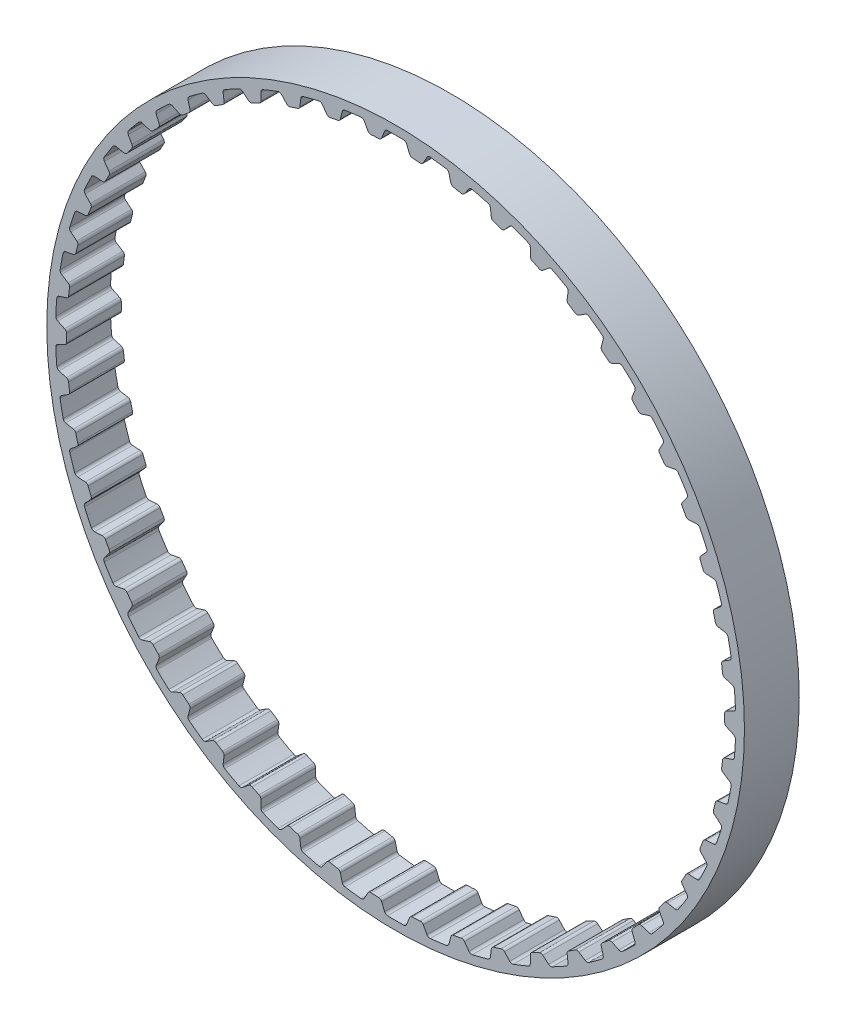
SolidWorks part; units mm, degrees
ref_plane "Front Plane" through (0, 0, 0) normal (0, 0, 1) x (1, 0, 0)
ref_plane "Top Plane" through (0, 0, 0) normal (0, 1, 0) x (1, 0, 0)
ref_plane "Right Plane" through (0, 0, 0) normal (1, 0, 0) x (0, 0, -1)
sketch "Sketch1" plane through (0, 0, 0) normal (0, 0, 1) x (1, 0, 0)
  line L0 (0, 0) -> (-2.3948, 38.0641) construction
  line L1 (0, 0) -> (2.3948, 38.0641) construction
  line L2 (2.3948, 38.0641) -> (-2.3948, 38.0641) construction
  line L3 (2.3948, 38.0641) -> (-2.3948, 38.0641) construction
  circle A0 centre (0, 0) radius 40.4254
  circle A1 centre (0, 0) radius 38.1394
  circle A2 centre (0, 0) radius 39.4094 construction
  dimension "OD" = 80.8508
  dimension "Angle Distance" = 7.2
  dimension "hs" = 2.286
  dimension "ht" = 1.27
extrude "Boss-Extrude1" add sketch "Sketch1" along normal mid plane 6.35
sketch "Sketch2" plane through (0, 0, 0) normal (0, 0, 1) x (1, 0, 0)
  line L1 (0, 40.4254) -> (0, 0) construction
  line L2 (-2.54, 38.7498) -> (2.54, 38.7498) construction
  line L4 (-1.6934, 38.1083) -> (-3.0962, 38.02)
  line L5 (-1.6934, 38.1083) -> (-1.1905, 39.3914)
  line L6 (-3.0962, 38.02) -> (-3.7559, 39.23)
  line L7 (0, 0) -> (-2.3948, 38.0641) construction
  line L8 (-1.1905, 39.3914) -> (-3.7559, 39.23) construction
  line L9 (1.1905, 39.3914) -> (3.7559, 39.23) construction
  line L10 (3.0962, 38.02) -> (3.7559, 39.23)
  line L11 (1.6934, 38.1083) -> (1.1905, 39.3914)
  line L12 (1.6934, 38.1083) -> (3.0962, 38.02)
  line L13 (0, 0) -> (15.4701, 37.3482) construction
  line L14 (-2.54, 38.7498) -> (-7.5765, 38.0867) construction
  line L15 (-5.0583, 38.4183) -> (0, 0) construction
  line L16 (-7.5765, 38.0867) -> (-7.4412, 37.4064) construction
  circle A0 centre (0, 0) radius 39.4094 construction
  circle A1 centre (0, 0) radius 39.4094
  circle A2 centre (0, 0) radius 38.7498 construction
  circle A4 centre (0, 0) radius 40.4254 construction
  circle A5 centre (0, 0) radius 38.1394 construction
  point P16 (-1.4419, 38.7498)
  point P20 (0, 38.7498)
  dimension "D1" = 22.5
  dimension "bt" = 2.5654
  dimension "b" = 50
  dimension "Pitch" = 5.08
sketch "Sketch3" plane through (0, 0, 0) normal (0, 0, 1) x (1, 0, 0)
  line L0 (-1.9413, 38.09) -> (1.9413, 38.09)
  line L2 (-1.6934, 38.1083) -> (-1.1905, 39.3914) construction
  line L3 (1.6934, 38.1083) -> (1.1905, 39.3914) construction
  line L5 (-1.6059, 38.3314) -> (-1.2826, 39.1564)
  line L7 (1.6059, 38.3314) -> (1.2826, 39.1564)
  arc A0 (1.6059, 38.3314) -> (1.9413, 38.09) centre (1.9606, 38.4705) ccw
  circle A1 centre (0, 0) radius 39.4094 construction
  arc A2 (0.937, 39.3983) -> (-0.937, 39.3983) centre (0, 0) ccw
  arc A3 (-1.6059, 38.3314) -> (-1.9413, 38.09) centre (-1.9606, 38.4705) cw
  arc A4 (1.2826, 39.1564) -> (0.937, 39.3983) centre (0.9279, 39.0174) ccw
  arc A5 (-1.2826, 39.1564) -> (-0.937, 39.3983) centre (-0.9279, 39.0174) cw
  circle A6 centre (0, 0) radius 38.1394 construction
  arc A7 (-1.9413, 38.09) -> (1.9413, 38.09) centre (0, 0) ccw construction
  dimension "ra" = 0.381
  dimension "rr" = 0.381
extrude "Cut-Extrude1" cut sketch "Sketch3" against normal mid plane 6.35
pattern_circular "CirPattern1" count 50 over 360 about axis through (0, 0, 0) along (0, 0, 1) of "Cut-Extrude1"
equation "\"D1@Cut-Extrude1\" = \"Width@Boss-Extrude1\""
